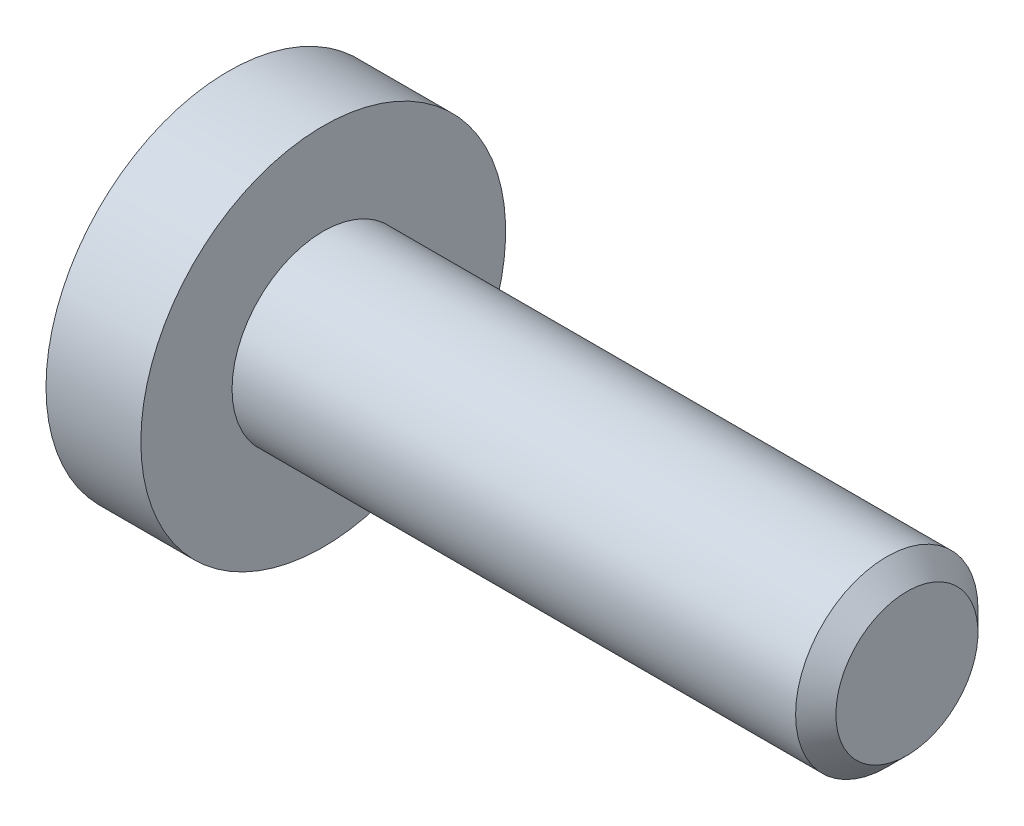
SolidWorks part; units mm, degrees
ref_plane "Plan de face" through (0, 0, 0) normal (0, 0, 1) x (1, 0, 0)
ref_plane "Plan de dessus" through (0, 0, 0) normal (0, 1, 0) x (1, 0, 0)
ref_plane "Plan de droite" through (0, 0, 0) normal (1, 0, 0) x (0, 0, -1)
ref_plane "Plan1" through (0, 0, 0) normal (0, 1, 0) x (1, 0, 0)
sketch "Esquisse1" plane through (0, 0, 0) normal (0, 1, 0) x (1, 0, 0)
  line L0 (-1.3, 0) -> (-1.3, 2.5)
  line L1 (-1.3, 2.5) -> (0, 2.5)
  line L2 (0, 2.5) -> (0, 1.25)
  line L3 (0, 1.25) -> (7.724, 1.25)
  line L4 (7.724, 1.25) -> (8, 0.974)
  line L5 (8, 0.974) -> (8, 0)
  line L6 (8, 0) -> (-1.3, 0)
  line L7 (8, 0) -> (-1.3, 0) construction
revolve "Révolution1" add sketch "Esquisse1" angle 360 about L7
cosmetic thread "Représentation de filetage1" parameters "D1"=6.6, "D2"=1.948
ref_plane "Plan2" through (0, 0, 0) normal (0, 0, 1) x (1, 0, 0)
sketch "Esquisse2" plane through (0, 0, 0) normal (0, 0, 1) x (1, 0, 0)
  line L0 (-1.3, 0) -> (-1.3, 0.7506)
  line L1 (-1.3, 0.7506) -> (-1.1994, 0.65)
  line L2 (-1.1994, 0.65) -> (0.2, 0.65)
  line L3 (0.2, 0.65) -> (0.5753, 0)
  line L4 (0.5753, 0) -> (-1.3, 0)
  line L5 (0.5753, 0) -> (-1.3, 0) construction
revolve "Enlèvement de matière-Révolution1" cut sketch "Esquisse2" angle 360 about L5
ref_plane "Plan3" through (-1.3, 0, 0) normal (1, 0, 0) x (0, 0, -1)
sketch "Esquisse3" plane through (-1.3, 0, 0) normal (1, 0, 0) x (0, 0, -1)
  line L0 (-0.65, 0.3753) -> (-0.65, -0.3753)
  line L1 (-0.65, -0.3753) -> (0, -0.7506)
  line L2 (0, -0.7506) -> (0.65, -0.3753)
  line L3 (0.65, -0.3753) -> (0.65, 0.3753)
  line L4 (0.65, 0.3753) -> (0, 0.7506)
  line L5 (0, 0.7506) -> (-0.65, 0.3753)
extrude "Enlèv. mat.-Extru.1" cut sketch "Esquisse3" along normal blind 1.5
